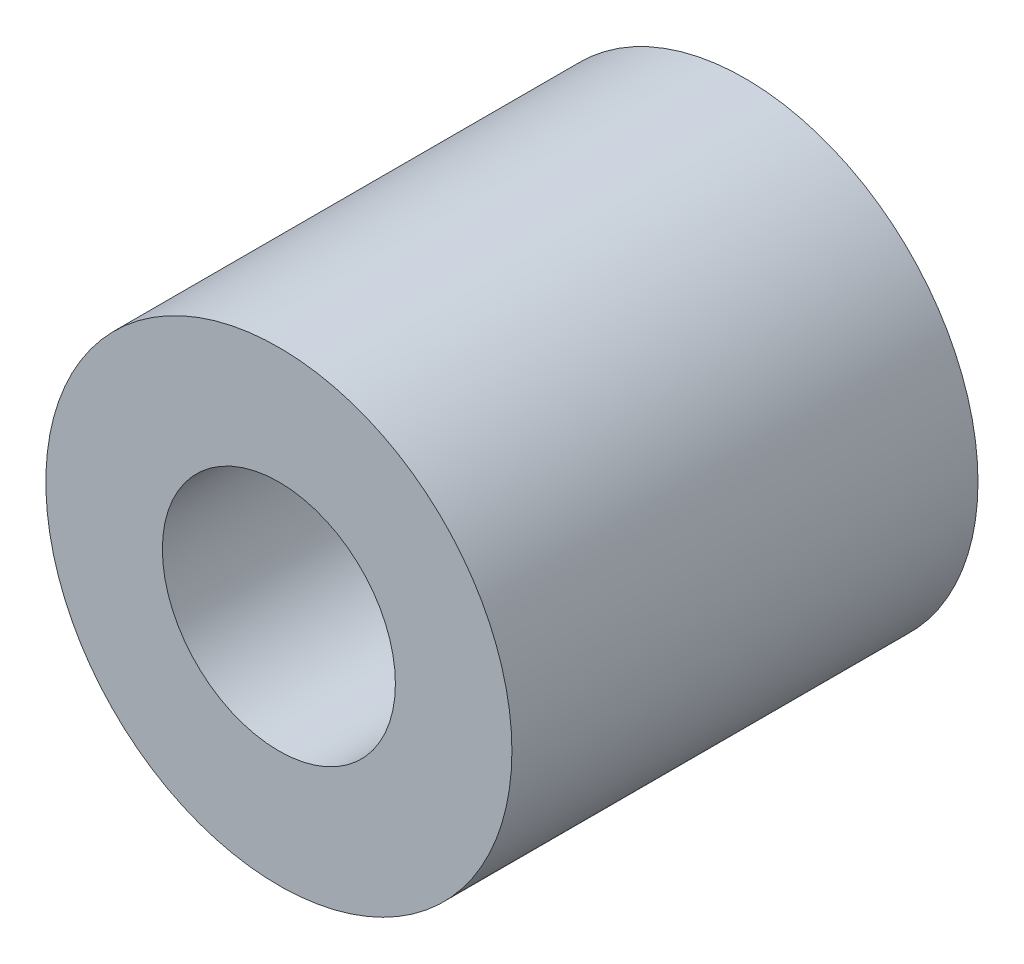
SolidWorks part; units mm, degrees
material "Aluminum Bronze"
ref_plane "Front Plane" through (0, 0, 0) normal (0, 0, 1) x (1, 0, 0)
ref_plane "Top Plane" through (0, 0, 0) normal (0, 1, 0) x (1, 0, 0)
ref_plane "Right Plane" through (0, 0, 0) normal (1, 0, 0) x (0, 0, -1)
sketch "Sketch1" plane through (0, 0, 0) normal (0, 0, 1) x (1, 0, 0)
  circle A0 centre (0, 0) radius 3.175
  circle A1 centre (0, 0) radius 1.5875
  dimension "D1" = 6.35
  dimension "D2" = 3.175
extrude "Boss-Extrude1" add sketch "Sketch1" along normal blind 6.35
